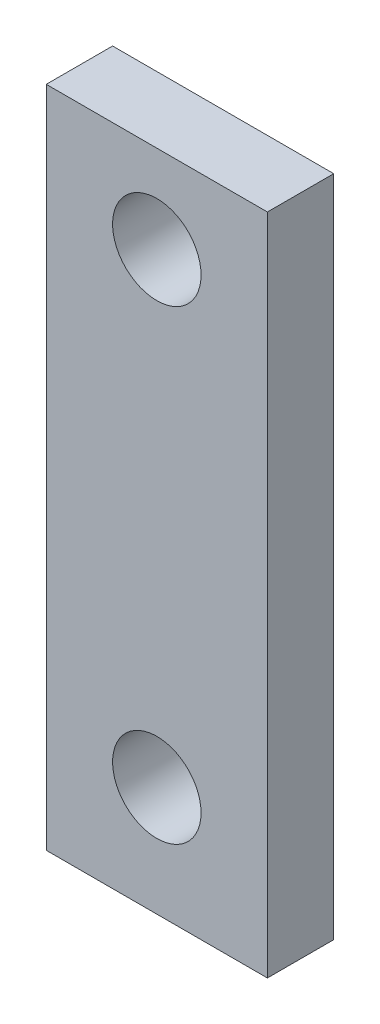
SolidWorks part; units mm, degrees
ref_plane "Front Plane" through (0, 0, 0) normal (0, 0, 1) x (1, 0, 0)
ref_plane "Top Plane" through (0, 0, 0) normal (0, 1, 0) x (1, 0, 0)
ref_plane "Right Plane" through (0, 0, 0) normal (1, 0, 0) x (0, 0, -1)
sketch "Sketch1" plane through (0, 0, 0) normal (0, 0, 1) x (1, 0, 0)
  line L1 (-5, -15) -> (5, -15)
  line L2 (-5, -15) -> (-5, 15)
  line L3 (-5, 15) -> (5, 15)
  line L4 (5, -15) -> (5, 15)
  line L5 (-5, -15) -> (5, 15) construction
  line L6 (-5, 15) -> (5, -15) construction
  point P0 (0, 0)
  dimension "D1" = 10
  dimension "D2" = 30
extrude "Boss-Extrude1" add sketch "Sketch1" along normal blind 3
sketch "Sketch2" plane through (0, 0, 3) normal (0, 0, 1) x (1, 0, 0)
  circle A0 centre (0, 11.0283) radius 2
  circle A1 centre (0, -10.0349) radius 2
  point P4 (0, 0)
  point P6 (0, 0)
  dimension "D1" = 4
extrude "Cut-Extrude1" cut sketch "Sketch2" against normal blind 10
